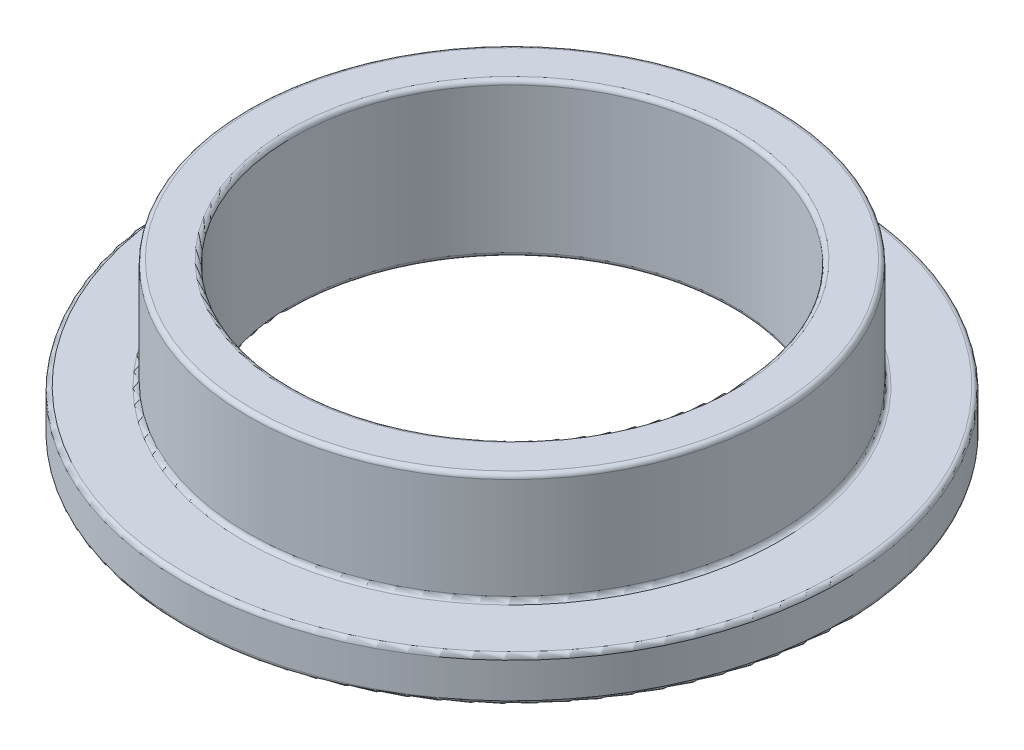
SolidWorks part; units mm, degrees
material "Commercial Bronze, UNS C22000 (90-10 Bronze)"
ref_plane "Front" through (0, 0, 0) normal (0, 0, 1) x (1, 0, 0)
ref_plane "Top" through (0, 0, 0) normal (0, 1, 0) x (1, 0, 0)
ref_plane "Right" through (0, 0, 0) normal (1, 0, 0) x (0, 0, -1)
sketch "Sketch1" plane through (0, 0, 0) normal (0, 1, 0) x (1, 0, 0)
  circle A0 centre (0, 0) radius 5
  circle A1 centre (0, 0) radius 6
  circle A2 centre (0, 0) radius 7.5
  dimension "ID" = 10
  dimension "OD" = 12
  dimension "FlangeOD" = 15
sketch "Sketch2" plane through (0, 0, 0) normal (1, 0, 0) x (0, 0, -1)
  line L0 (7.5, 0) -> (7.5, 1) construction
  line L1 (-6, 0) -> (-6, 3.5) construction
  line L8 (0, 0) -> (0, 3.5) construction
  point P5 (-7.5, 0)
  dimension "Flange Thickness" = 1
  dimension "Length" = 3.5
sketch "Sketch3" plane through (0, 0, 0) normal (0, 1, 0) x (1, 0, 0)
  circle A0 centre (0, 0) radius 5 construction
  circle A1 centre (0, 0) radius 6 construction
  circle A2 centre (0, 0) radius 5
  circle A3 centre (0, 0) radius 6
extrude "Boss-Extrude1" add sketch "Sketch3" along normal up to vertex (3.5 mm away) up to point (0, 3.5, 6)
sketch "Sketch4" plane through (0, 0, 0) normal (0, 1, 0) x (1, 0, 0)
  circle A0 centre (0, 0) radius 7.5 construction
  circle A1 centre (0, 0) radius 6 construction
  circle A2 centre (0, 0) radius 7.5
  circle A3 centre (0, 0) radius 6
extrude "Boss-Extrude2" add sketch "Sketch4" along normal up to vertex (1 mm away) up to point (0, 1, -7.5)
fillet "Fillet1" radius 0.1 6 edges at (0, 0, 5) (0, 0, 7.5) (0, 1, 6) (0, 1, 7.5) (0, 3.5, 5) (0, 3.5, 6)
equation "\"D1@Fillet1\"=(\"OD@Sketch1\"-\"ID@Sketch1\")*.05"
